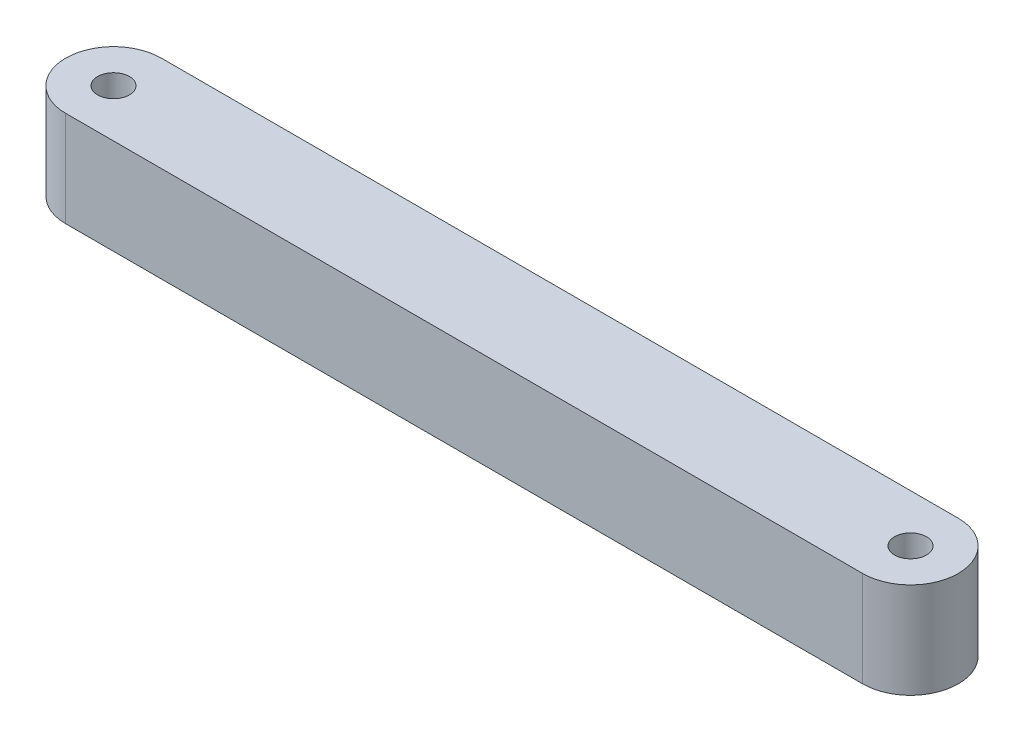
SolidWorks part; units mm, degrees
ref_plane "Front Plane" through (0, 0, 0) normal (0, 0, 1) x (1, 0, 0)
ref_plane "Top Plane" through (0, 0, 0) normal (0, 1, 0) x (1, 0, 0)
ref_plane "Right Plane" through (0, 0, 0) normal (1, 0, 0) x (0, 0, -1)
sketch "Sketch1" plane through (0, 0, 0) normal (0, 1, 0) x (1, 0, 0)
  line L0 (0, 0) -> (34315.2938, 0) construction
  line L1 (0, 0) -> (0, 34315.2938) construction
  line L2 (-79.375, -9.525) -> (79.375, -9.525)
  line L3 (-79.375, 9.525) -> (79.375, 9.525)
  arc A1 (-79.375, 9.525) -> (-79.375, -9.525) centre (-79.375, 0) ccw
  arc A2 (79.375, 9.525) -> (79.375, -9.525) centre (79.375, 0) cw
  circle A3 centre (-79.375, 0) radius 3.175
  circle A4 centre (79.375, 0) radius 3.175
  point P2 (-88.9, 0)
  point P7 (88.9, 0)
  point P13 (0, -9.525)
  point P16 (0, 9.525)
  dimension "D2" = 177.8
  dimension "D3" = 6.35
  dimension "D1" = 19.05
extrude "Boss-Extrude1" add sketch "Sketch1" along normal blind 19.05
